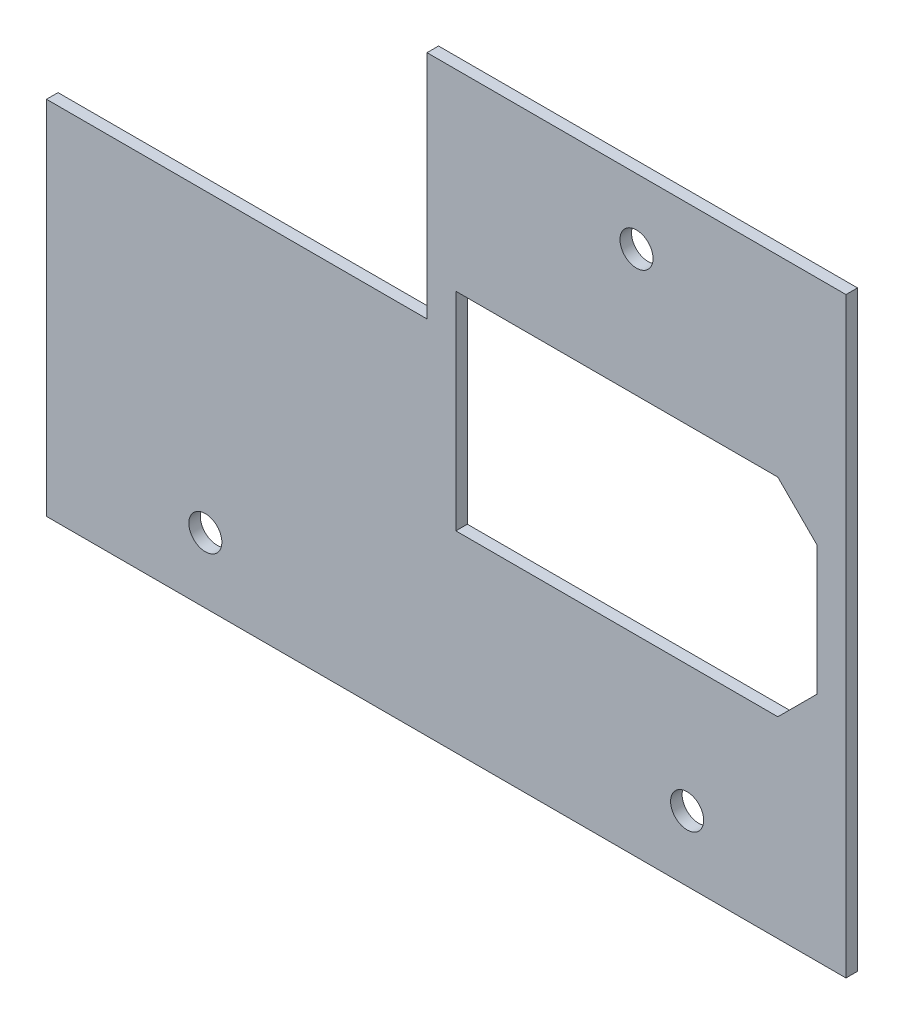
SolidWorks part; units mm, degrees
ref_plane "Plan de face" through (0, 0, 0) normal (0, 0, 1) x (1, 0, 0)
ref_plane "Plan de dessus" through (0, 0, 0) normal (0, 1, 0) x (1, 0, 0)
ref_plane "Plan de droite" through (0, 0, 0) normal (1, 0, 0) x (0, 0, -1)
sketch "Esquisse1" plane through (0, 0, -20) normal (0, 0, 1) x (1, 0, 0)
  line L0 (148.0031, 65.5289) -> (148.0031, -11.4711)
  line L1 (93.5, 65.5289) -> (148.0031, 65.5289)
  line L2 (44, 35.5289) -> (44, -11.4711)
  line L3 (0, 65.5289) -> (300, 65.5289) construction
  line L5 (93.5, 65.5289) -> (93.5, 35.5289)
  line L6 (93.5, 35.5289) -> (44, 35.5289)
  line L7 (92.5, 46.0289) -> (92.5, 57.0289) construction
  line L9 (151.0031, 47.0289) -> (151.0031, 63.0289) construction
  line L10 (91.5, 36.0289) -> (50, 36.0289) construction
  line L11 (44, -11.4711) -> (148.0031, -11.4711)
  line L12 (300, -11.4711) -> (0, -11.4711) construction
  dimension "D1" = 1
  dimension "D2" = 3
  dimension "D3" = 0.5
  dimension "D4" = 47
extrude "Boss.-Extru.1" add sketch "Esquisse1" against normal blind 1.5
hole_wizard "Dégagement M41" positions "Esquisse4" profile "Esquisse3" hole size "M4" standard "Din"
sketch "Esquisse4" plane through (0, 0, -21.5) normal (0, 0, -1) x (-1, 0, 0)
  line L0 (-120.7516, 65.5289) -> (-120.7516, 57.0289) construction
  line L1 (-148.0031, 65.5289) -> (-93.5, 65.5289) construction
  line L3 (-127.3394, -2.9711) -> (-64.6637, -2.9711) construction
  line L4 (-96.0016, -2.9711) -> (-96.0016, -11.4711) construction
  line L5 (-44, -11.4711) -> (-148.0031, -11.4711) construction
  point P0 (-120.7516, 57.0289)
  point P2 (-127.3394, -2.9711)
  point P4 (-64.6637, -2.9711)
  dimension "D1" = 8.5
  dimension "D2" = 8.5
sketch "Esquisse3" plane through (120.7516, 57.0289, -21.5) normal (1, 0, 0) x (0, 1, 0)
  line L0 (0, 0) -> (0, 24)
  line L1 (0, 24) -> (2.15, 24)
  line L2 (2.15, 24) -> (2.15, 0)
  line L5 (2.15, 0) -> (0, 0)
  line L10 (0, 24) -> (-2.15, 24) construction
  line L11 (0, -6.35) -> (0, 107.95) construction
  dimension "Diamètre du perçage" = 4.3
  dimension "Profondeur du perçage" = 24
  dimension "Angle de pointe" = 180
sketch "Esquisse5" plane through (0, 0, -21.5) normal (0, 0, -1) x (-1, 0, 0)
  line L0 (-144.2516, 27.0289) -> (-97.2516, 27.0289) construction
  line L1 (-97.2516, 40.5289) -> (-139.1391, 40.5289)
  line L2 (-97.2516, 40.5289) -> (-97.2516, 13.5289)
  line L3 (-97.2516, 13.5289) -> (-139.1391, 13.5289)
  line L4 (-144.2516, 35.4165) -> (-144.2516, 18.6414)
  line L5 (-120.7516, 27.0289) -> (-120.7516, 65.5289) construction
  line L6 (-148.0031, 65.5289) -> (-93.5, 65.5289) construction
  line L8 (-139.1391, 40.5289) -> (-144.2516, 35.4165)
  line L9 (-139.1391, 13.5289) -> (-144.2516, 18.6414)
  line L10 (-144.2516, 27.0289) -> (-148.0031, 27.0289) construction
  line L11 (-148.0031, -11.4711) -> (-148.0031, 65.5289) construction
  point P1 (-144.2516, 13.5289)
  point P3 (-144.2516, 40.5289)
  dimension "D1" = 27
  dimension "D2" = 47
extrude "Enlèv. mat.-Extru.1" cut sketch "Esquisse5" against normal through all
